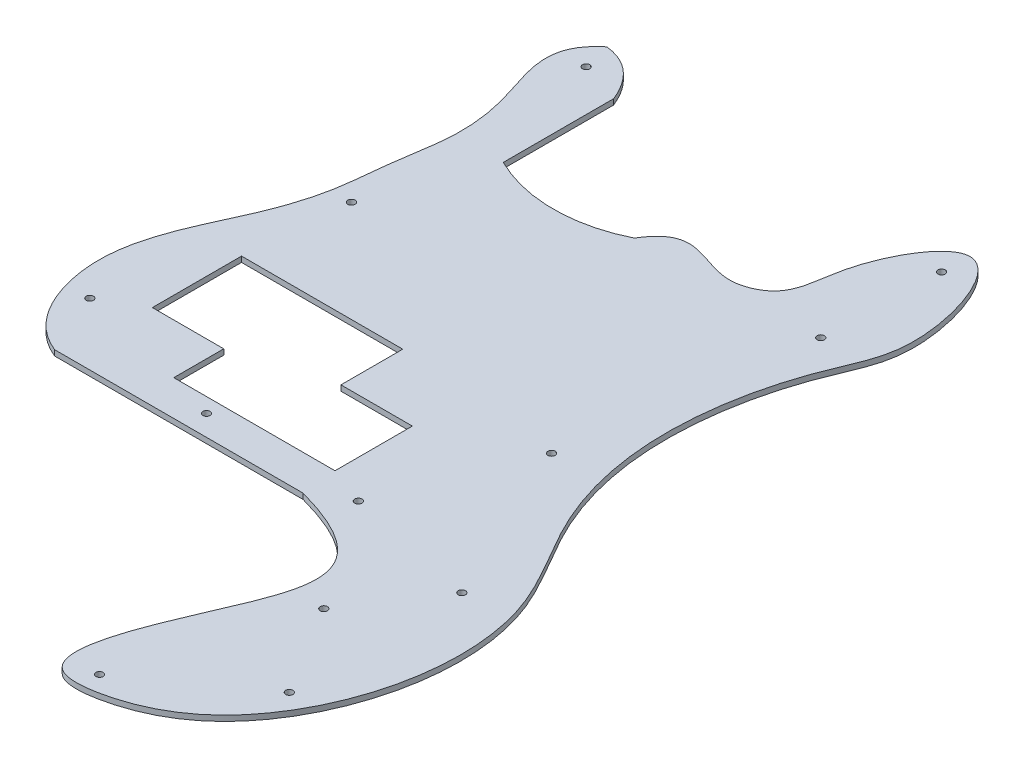
SolidWorks part; units mm, degrees
ref_plane "Front Plane" through (0, 0, 0) normal (0, 0, 1) x (1, 0, 0)
ref_plane "Top Plane" through (0, 0, 0) normal (0, 1, 0) x (1, 0, 0)
ref_plane "Right Plane" through (0, 0, 0) normal (1, 0, 0) x (0, 0, -1)
sketch "Sketch1" plane through (0, 0, 0) normal (0, 1, 0) x (1, 0, 0)
  line L0 (0, 0) -> (114.3, 0)
  line L1 (88.9, 0) -> (88.9, 254) construction
  line L2 (28.575, 228.6) -> (28.575, 177.8)
  line L3 (58.7375, 238.2047) -> (58.7375, 170.688) construction
  line L4 (88.9, 177.8) -> (88.9, 186.182)
  arc A0 (28.575, 177.8) -> (88.9, 177.8) centre (58.7375, 238.2047) ccw
  circle A1 centre (60.325, 9.525) radius 1.6764
  circle A2 centre (130.175, 9.525) radius 1.6764
  circle A3 centre (-12.3825, 28.575) radius 1.6764
  circle A4 centre (9.525, 127) radius 1.6764
  circle A5 centre (9.525, 234.95) radius 1.6764
  circle A6 centre (173.0375, 234.95) radius 1.6764
  circle A7 centre (171.45, 180.975) radius 1.6764
  circle A8 centre (155.575, 73.025) radius 1.6764
  circle A9 centre (190.5, -3.175) radius 1.6764
  circle A10 centre (190.5, -82.55) radius 1.6764
  circle A11 centre (139.7, -119.0625) radius 1.6764
  circle A12 centre (165.1, -41.275) radius 1.6764
  spline S0 degree 3 poles (0, 0) (-11.53, 4.5145) (-23.5981, 21.7649) (-27.1419, 51.1961) (-19.6131, 77.0698) (-7.4978, 100.9452) (1.0987, 126.4824) (2.5386, 152.4514) (7.7782, 177.7738) (3.4996, 210.5141) (-10.048, 234.3249) (6.35, 247.65) knots 0 0 0 0 0.130339 0.226964 0.325793 0.430447 0.530898 0.627523 0.724148 0.820773 1 1 1 1
  spline S1 degree 2 poles (6.35, 247.65) (21.4241, 246.03) (28.575, 228.6) knots 0 0 0 1 1 1
  spline S2 degree 3 poles (114.3, 0) (170.6232, -15.3245) (142.7785, -51.0148) (117.0724, -130.8654) (166.9104, -124.7473) (211.27, -85.6481) (223.2542, -5.8432) (185.8262, 45.0847) (168.8927, 100.7019) (177.4566, 154.683) (201.0165, 201.5584) (177.94, 271.8374) (147.1181, 218.1363) (148.1281, 189.8298) (118.7164, 176.4979) (100.9796, 198.2106) (88.9, 177.8) knots 0 0 0 0 0.148093 0.210363 0.240169 0.32198 0.461111 0.528033 0.586689 0.706182 0.742682 0.823051 0.881913 0.917689 0.939313 1 1 1 1
  point P6 (88.9, 12.7)
  point P8 (88.9, 25.4)
  point P10 (88.9, 50.8)
  point P12 (88.9, 76.2)
  point P13 (88.9, 177.8)
  point P15 (88.9, 177.8)
  point P16 (88.9, 101.6)
  point P17 (88.9, 127)
  point P18 (88.9, 152.4)
  point P19 (88.9, 247.65)
  point P20 (88.9, 203.2)
  point P40 (88.9, 228.6)
  dimension "D27" = 3.3528
  dimension "D39" = 50.8
  dimension "D40" = 119.0625
  dimension "D41" = 101.6
  dimension "D42" = 82.55
  dimension "D47" = 180.975
  dimension "D48" = 82.55
  dimension "D49" = 84.1375
  dimension "D1" = 114.3
  dimension "D2" = 25.4
  dimension "D3" = 12.7
  dimension "D4" = 25.4
  dimension "D5" = 50.8
  dimension "D6" = 76.2
  dimension "D8" = 25.4
  dimension "D9" = 25.4
  dimension "D10" = 254
  dimension "D11" = 25.4
  dimension "D12" = 104.775
  dimension "D13" = 111.125
  dimension "D14" = 114.3
  dimension "D15" = 107.95
  dimension "D16" = 96.8375
  dimension "D17" = 88.9
  dimension "D18" = 85.725
  dimension "D19" = 82.55
  dimension "D20" = 85.725
  dimension "D21" = 92.075
  dimension "D22" = 247.65
  dimension "D23" = 82.55
  dimension "D24" = 60.325
  dimension "D25" = 7.112
  dimension "D26" = 8.382
  dimension "D28" = 79.375
  dimension "D29" = 234.95
  dimension "D30" = 79.375
  dimension "D31" = 127
  dimension "D32" = 28.575
  dimension "D33" = 101.2825
  dimension "D34" = 28.575
  dimension "D35" = 9.525
  dimension "D36" = 69.85
  dimension "D37" = 41.275
  dimension "D38" = 76.2
  dimension "D43" = 101.6
  dimension "D44" = 3.175
  dimension "D45" = 66.675
  dimension "D46" = 73.025
  dimension "D7" = 6
extrude "Boss-Extrude1" add sketch "Sketch1" along normal blind 2.54 contours L0 S2 A0 L2 S1 S0 A1 A2 A3 A4 A5 A7 A8 A9 A10 A11 A12
sketch "Sketch2" plane through (0, 2.54, 0) normal (0, 1, 0) x (1, 0, 0)
  line L0 (38.546, 16.256) -> (112.7098, 16.256)
  line L1 (112.7098, 16.256) -> (112.7098, 51.838)
  line L2 (112.7098, 51.838) -> (79.8616, 51.838)
  line L3 (79.8616, 51.838) -> (79.8616, 80.2704)
  line L4 (79.8616, 80.2704) -> (5.6978, 80.2704)
  line L5 (5.6978, 80.2704) -> (5.6978, 39.2435)
  line L6 (5.6978, 39.2435) -> (38.546, 39.2435)
  line L7 (38.546, 39.2435) -> (38.546, 16.256)
  point P0 (43.7338, 16.256)
  point P4 (0, 0)
  dimension "D1" = 74.1638
  dimension "D2" = 32.8482
  dimension "D3" = 22.9875
  dimension "D4" = 64.0144
  dimension "D5" = 35.582
extrude "Cut-Extrude1" cut sketch "Sketch2" against normal through all
